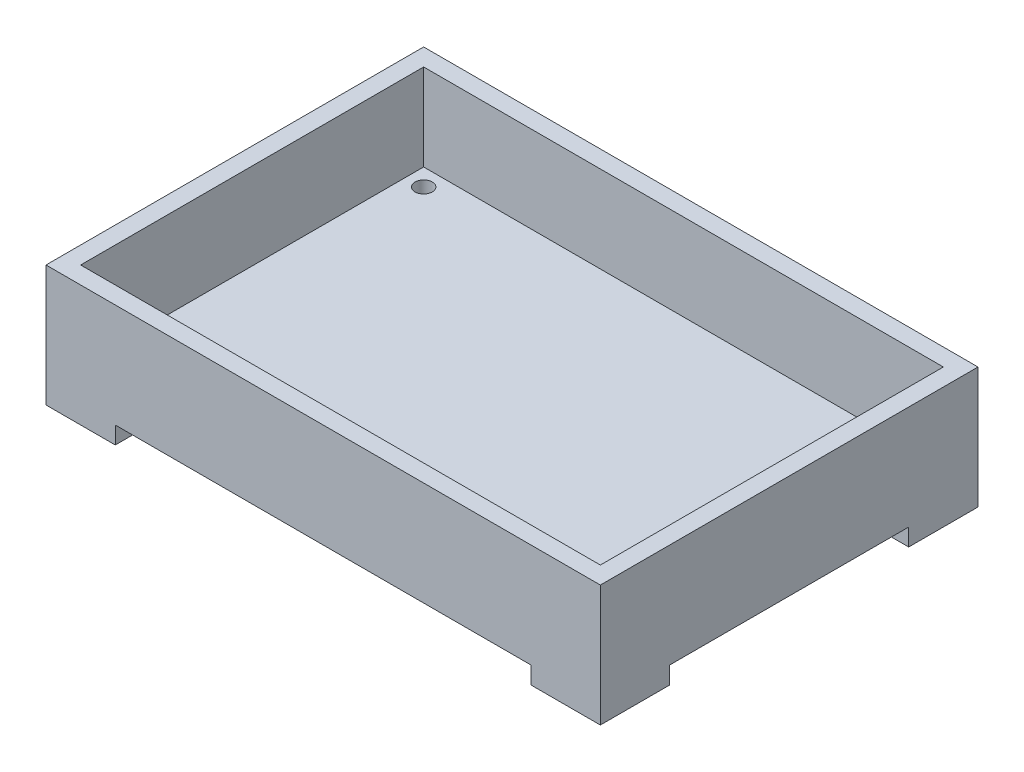
SolidWorks part; units mm, degrees
ref_plane "Front Plane" through (0, 0, 0) normal (0, 0, 1) x (1, 0, 0)
ref_plane "Top Plane" through (0, 0, 0) normal (0, 1, 0) x (1, 0, 0)
ref_plane "Right Plane" through (0, 0, 0) normal (1, 0, 0) x (0, 0, -1)
sketch "Sketch1" plane through (0, 0, 0) normal (0, 1, 0) x (1, 0, 0)
  line L1 (-101.6, -69.215) -> (101.6, -69.215)
  line L2 (-101.6, -69.215) -> (-101.6, 69.215)
  line L3 (-101.6, 69.215) -> (101.6, 69.215)
  line L4 (101.6, -69.215) -> (101.6, 69.215)
  line L5 (-101.6, -69.215) -> (101.6, 69.215) construction
  line L6 (-101.6, 69.215) -> (101.6, -69.215) construction
  point P0 (0, 0)
  dimension "D1" = 203.2
  dimension "D2" = 138.43
extrude "Boss-Extrude2" add sketch "Sketch1" along normal blind 38.1
shell "Shell1" thickness 6.35
sketch "Sketch2" plane through (0, 0, 0) normal (0, -1, 0) x (1, 0, 0)
  line L1 (-101.6, 69.215) -> (-76.2, 69.215)
  line L2 (-101.6, 69.215) -> (-101.6, 43.815)
  line L3 (-101.6, 43.815) -> (-76.2, 43.815)
  line L4 (-76.2, 69.215) -> (-76.2, 43.815)
  line L6 (-101.6, 69.215) -> (101.6, 69.215) construction
  line L7 (-101.6, -69.215) -> (-101.6, 69.215) construction
  dimension "D1" = 25.4
  dimension "D2" = 25.4
extrude "Boss-Extrude4" add sketch "Sketch2" along normal blind 6.35
sketch "Sketch3" plane through (0, 6.35, 0) normal (0, 1, 0) x (1, 0, 0)
  line L0 (-95.25, -62.865) -> (95.25, -62.865) construction
  line L1 (-95.25, 62.865) -> (-95.25, -62.865) construction
  circle A0 centre (-88.9, -56.515) radius 3.175
  dimension "D1" = 6.35
  dimension "D2" = 6.35
  dimension "D3" = 6.35
extrude "Cut-Extrude1" cut sketch "Sketch3" against normal through all
mirror "Mirror3" about plane through (0, 0, 0) normal (1, 0, 0) of "Cut-Extrude1", "Boss-Extrude4"
mirror "Mirror4" about plane through (0, 0, 0) normal (0, 0, 1) of "Mirror3", "Boss-Extrude4", "Cut-Extrude1"
